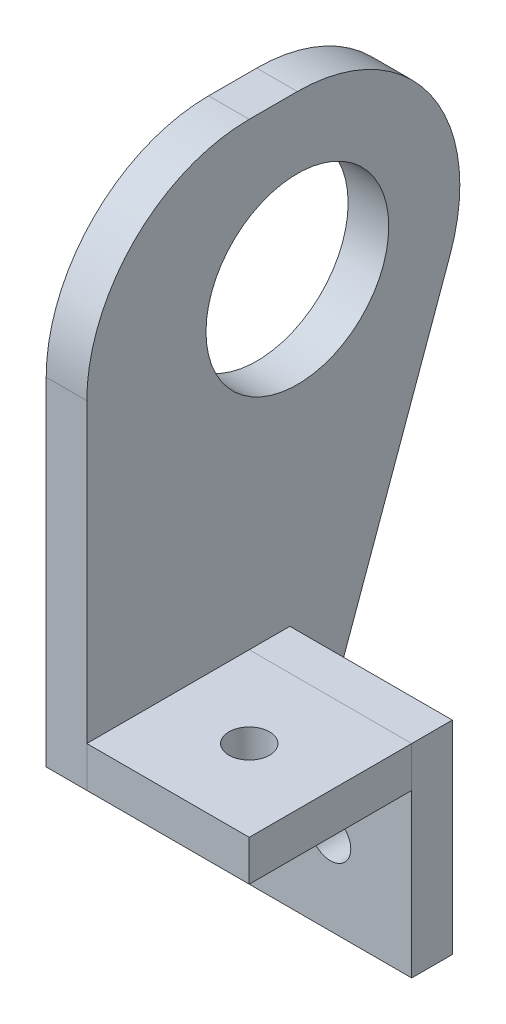
SolidWorks part; units mm, degrees
material "6061-T6 (SS)"
ref_plane "Front Plane" through (0, 0, 0) normal (0, 0, 1) x (1, 0, 0)
ref_plane "Top Plane" through (0, 0, 0) normal (0, 1, 0) x (1, 0, 0)
ref_plane "Right Plane" through (0, 0, 0) normal (1, 0, 0) x (0, 0, -1)
sketch "Sketch1" plane through (0, 0, 0) normal (1, 0, 0) x (0, 0, -1)
  line L0 (0, 25.4) -> (-32.925, 25.4)
  line L1 (-32.925, 25.4) -> (-32.925, -52.775)
  line L2 (-7.525, -78.175) -> (-1.175, -78.175)
  line L3 (-1.175, -78.175) -> (23.8955, -8.6119)
  line L4 (-32.925, -52.775) -> (-32.925, 232.975) construction
  line L5 (-7.525, -78.175) -> (-32.925, -78.175) construction
  line L6 (-7.525, -78.175) -> (-7.525, -54.3625)
  line L7 (-9.1125, -52.775) -> (-32.925, -52.775)
  circle A0 centre (0, 0) radius 14.2875
  arc A1 (23.8955, -8.6119) -> (0, 25.4) centre (0, 0) ccw
  arc A2 (-7.525, -54.3625) -> (-9.1125, -52.775) centre (-9.1125, -54.3625) ccw
  point P9 (-7.525, -52.775)
  dimension "D1" = 28.575
  dimension "D2" = 25.4
  dimension "D5" = 1.5875
  dimension "D3" = 31.75
  dimension "D4" = 25.4
extrude "Boss-Extrude1" add sketch "Sketch1" along normal blind 6.35
sketch "Sketch2" plane through (6.35, 0, 0) normal (1, 0, 0) x (0, 0, -1)
  line L0 (-7.525, -54.3625) -> (-7.525, -78.175) construction
  line L1 (-32.925, -52.775) -> (-7.525, -52.775)
  line L2 (-32.925, -52.775) -> (-32.925, -46.425)
  line L3 (-32.925, -46.425) -> (-7.525, -46.425)
  line L4 (-7.525, -52.775) -> (-7.525, -46.425)
  dimension "D1" = 6.35
extrude "Boss-Extrude2" add sketch "Sketch2" along normal blind 25.4 separate body
fillet "Fillet1" radius 25.4 1 edges at (3.175, 25.4, 32.925)
sketch "Sketch3" plane through (6.35, 0, 0) normal (1, 0, 0) x (0, 0, -1)
  line L1 (-1.175, -78.175) -> (-7.525, -78.175)
  line L2 (-1.175, -78.175) -> (-1.175, -46.425)
  line L3 (-1.175, -46.425) -> (-7.525, -46.425)
  line L4 (-7.525, -78.175) -> (-7.525, -46.425)
extrude "Boss-Extrude3" add sketch "Sketch3" along normal blind 25.4 separate body
sketch "Sketch4" plane through (0, -52.775, 0) normal (0, -1, 0) x (1, 0, 0)
  line L0 (19.05, 32.925) -> (19.05, 7.525) construction
  line L1 (31.75, 32.925) -> (6.35, 32.925) construction
  line L2 (31.75, 7.525) -> (6.35, 7.525) construction
  circle A0 centre (19.05, 20.225) radius 3.175
  dimension "D1" = 6.35
extrude "Cut-Extrude1" cut sketch "Sketch4" against normal through all
sketch "Sketch5" plane through (0, 0, 7.525) normal (0, 0, 1) x (1, 0, 0)
  line L0 (6.35, -52.775) -> (31.75, -78.175) construction
  circle A0 centre (19.05, -65.475) radius 3.175
  dimension "D1" = 6.35
extrude "Cut-Extrude2" cut sketch "Sketch5" against normal through all
sketch "Sketch6" [suppressed] plane through (0, 0, 0) normal (1, 0, 0) x (0, 0, -1)
  line L0 (-32.925, -52.775) -> (-7.525, -52.775)
  line L1 (-32.925, -52.775) -> (-7.525, -52.775) construction
  line L2 (0, 25.4) -> (-32.925, 25.4)
  line L3 (-32.925, 25.4) -> (-32.925, -52.775)
  line L4 (-7.525, -52.775) -> (-7.525, -48.0125)
  line L5 (-7.525, -48.0125) -> (19.338, -16.4682)
  line L6 (-32.925, -109.925) -> (-32.925, -78.175) construction
  circle A0 centre (0, 0) radius 25.4 construction
  circle A1 centre (0, 0) radius 14.2875
  arc A2 (0, 25.4) -> (19.338, -16.4682) centre (0, 0) cw
  dimension "D1" = 28.575
  dimension "D2" = 50.8
  dimension "D3" = 25.4
  dimension "D4" = 4.7625
base flange "Base-Flange2" [suppressed] sketch "Sketch6" thickness 3.175 reverse thickness direction no parameters "D1"=0.7366
edge flange "Edge-Flange1" sketch "Sketch18" flange angle 90 flange position material inside bend radius 0.7366 thickness 3.175
sketch "Sketch18" [suppressed] plane through (0, -33.725, 0) normal (0, -1, 0) x (0, 0, -1)
  line L2 (-32.925, 0) -> (-32.925, 25.4)
  line L3 (-32.925, 25.4) -> (-7.525, 25.4)
  line L4 (-7.525, 25.4) -> (-7.525, 0)
  line L5 (-32.925, 0) -> (-7.525, 0) construction
  line L6 (-32.925, 0) -> (-7.525, 0)
bend "EdgeBend1" [suppressed] bend radius 0.7366 bend angle 90 parameters "D5"=1, "D6"=10, "D7"=25.4
sketch "Sketch22" [suppressed] plane through (0, -30.55, 0) normal (0, 1, 0) x (1, 0, 0)
  line L0 (0, -32.925) -> (25.4, -7.525) construction
  circle A0 centre (12.7, -20.225) radius 3.175
  dimension "D1" = 6.35
extrude "Cut-Extrude3" [suppressed] cut sketch "Sketch22" against normal through all
edge flange "Edge-Flange2" sketch "Sketch21" flange angle 90 flange position material inside bend radius 0.7366 thickness 3.175
sketch "Sketch21" [suppressed] plane through (-3.175, -52.775, 0) normal (0, -1, 0) x (0, 0, 1)
  line L0 (32.925, 0) -> (7.525, 0) construction
  line L1 (32.925, 0) -> (7.525, 0)
  line L2 (7.525, 0) -> (7.525, 25.4)
  line L3 (7.525, 25.4) -> (32.925, 25.4)
  line L4 (32.925, 25.4) -> (32.925, 0)
bend "EdgeBend2" [suppressed] bend radius 0.7366 bend angle 90 parameters "D5"=1, "D6"=10, "D7"=25.4
sketch "Sketch23" [suppressed] plane through (0, -49.6, 0) normal (0, 1, 0) x (1, 0, 0)
  line L0 (-28.575, -7.525) -> (-3.175, -32.925) construction
  circle A0 centre (-15.875, -20.225) radius 3.175
  dimension "D1" = 6.35
extrude "Cut-Extrude4" [suppressed] cut sketch "Sketch23" against normal through all
fillet "Fillet2" [suppressed] radius 25.4
sketch "Sketch24" [suppressed] plane through (0, 0, 0) normal (1, 0, 0) x (0, 0, -1)
  line L1 (-7.525, -28.2259) -> (-2.7934, -28.2259)
  line L2 (-7.525, -28.2259) -> (-7.525, -29.262)
  line L3 (-7.525, -29.262) -> (-2.7934, -29.262)
  line L4 (-2.7934, -28.2259) -> (-2.7934, -29.262)
extrude "Cut-Extrude5" [suppressed] cut sketch "Sketch24" against normal through all
fillet "Fillet3" [suppressed] radius 25.4
fillet "Fillet4" [suppressed] radius 1.5875
sketch "Bend-Lines3" [suppressed] plane through (0, 0, 0) normal (0, 1, 0) x (1, 0, 0)
sketch "Bounding-Box3" [suppressed] plane through (0, 0, 0) normal (0, 1, 0) x (1, 0, 0)
sheet metal parameters "Sheet-Metal7" [suppressed] thickness 3.175 parameters "D1"=0.7366
flat pattern "Flat-Pattern14"
sketch "Bend-Lines4" [suppressed] plane through (0, 0, 0) normal (0, 1, 0) x (1, 0, 0)
sketch3d "Bounding-Box4" [suppressed]
  line L0 (-29.3589, -46.2064, 0) -> (-29.3589, 25.4, 0) construction
  line L1 (25.4, -46.2064, 0) -> (25.4, 25.4, 0) construction
  line L2 (-29.3589, -46.2064, 0) -> (25.4, -46.2064, 0) construction
  line L3 (-29.3589, 25.4, 0) -> (25.4, 25.4, 0) construction
sheet metal parameters "Sheet-Metal8" [suppressed] thickness 3.175 parameters "D1"=0.7366
flat pattern "Flat-Pattern14"
sketch "Bend-Lines4" [suppressed] plane through (0, 0, 0) normal (1, 0, 0) x (0, 0, -1)
  line L0 (-29.3589, -44.1201) -> (-3.9589, -44.1201) construction
  line L1 (-29.3589, -44.1201) -> (-3.9589, -44.1201) construction
sketch3d "Bounding-Box4" [suppressed]
  line L0 (-29.3589, -70.6089, 0) -> (-29.3589, 25.4, 0) construction
  line L1 (25.4, -70.6089, 0) -> (25.4, 25.4, 0) construction
  line L2 (-29.3589, -70.6089, 0) -> (25.4, -70.6089, 0) construction
  line L3 (-29.3589, 25.4, 0) -> (25.4, 25.4, 0) construction
bend of the flat pattern "Flatten-<EdgeBend1>1" [suppressed]
sheet metal parameters "Sheet-Metal9" [suppressed] thickness 3.175 parameters "D1"=0.7366
flat pattern "Flat-Pattern14"
sketch "Bend-Lines4" [suppressed] plane through (0, 0, 0) normal (1, 0, 0) x (0, 0, -1)
  line L0 (-29.3589, -44.1201) -> (-3.9589, -44.1201) construction
  line L1 (-29.3589, -44.1201) -> (-3.9589, -44.1201) construction
sketch3d "Bounding-Box4" [suppressed]
  line L0 (-29.3589, -70.6089, 0) -> (-29.3589, 25.4, 0) construction
  line L1 (25.4, -70.6089, 0) -> (25.4, 25.4, 0) construction
  line L2 (-29.3589, -70.6089, 0) -> (25.4, -70.6089, 0) construction
  line L3 (-29.3589, 25.4, 0) -> (25.4, 25.4, 0) construction
bend of the flat pattern "Flatten-<EdgeBend2>1" [suppressed]
sheet metal parameters "Sheet-Metal10" [suppressed] thickness 3.175 parameters "D1"=0.7366
flat pattern "Flat-Pattern14"
sketch "Bend-Lines4" [suppressed] plane through (0, 0, 0) normal (1, 0, 0) x (0, 0, -1)
  line L0 (-32.925, -31.6387) -> (-7.525, -31.6387) construction
  line L1 (-32.925, -31.6387) -> (-7.525, -31.6387) construction
sketch3d "Bounding-Box4" [suppressed]
  line L0 (-32.925, -58.1275, 0) -> (-32.925, 25.4, 0) construction
  line L1 (25.4, -58.1275, 0) -> (25.4, 25.4, 0) construction
  line L2 (-32.925, -58.1275, 0) -> (25.4, -58.1275, 0) construction
  line L3 (-32.925, 25.4, 0) -> (25.4, 25.4, 0) construction
bend of the flat pattern "Flatten-<EdgeBend1>1" [suppressed]
sheet metal parameters "Sheet-Metal11" [suppressed] thickness 3.175 parameters "D1"=0.7366
flat pattern "Flat-Pattern14"
sketch "Bend-Lines4" [suppressed] plane through (0, 0, 0) normal (1, 0, 0) x (0, 0, -1)
  line L0 (-32.925, -50.6887) -> (-7.525, -50.6887) construction
  line L1 (-32.925, -50.6887) -> (-7.525, -50.6887) construction
sketch3d "Bounding-Box4" [suppressed]
  line L0 (-32.925, -77.1775, 0) -> (-32.925, 25.4, 0) construction
  line L1 (25.4, -77.1775, 0) -> (25.4, 25.4, 0) construction
  line L2 (-32.925, -77.1775, 0) -> (25.4, -77.1775, 0) construction
  line L3 (-32.925, 25.4, 0) -> (25.4, 25.4, 0) construction
bend of the flat pattern "Flatten-<EdgeBend2>1" [suppressed]
sheet metal parameters "Sheet-Metal14" [suppressed] thickness 3.175 parameters "D1"=0.7366
flat pattern "Flat-Pattern14"
sketch "Bend-Lines4" [suppressed] plane through (0, 0, 0) normal (1, 0, 0) x (0, 0, -1)
  line L2 (-32.925, -31.6387) -> (-7.525, -31.6387) construction
  line L3 (-32.925, -31.6387) -> (-7.525, -31.6387) construction
sketch3d "Bounding-Box4" [suppressed]
  line L0 (-32.925, -58.1275, 0) -> (-32.925, 25.4, 0) construction
  line L1 (25.4, -58.1275, 0) -> (25.4, 25.4, 0) construction
  line L2 (-32.925, -58.1275, 0) -> (25.4, -58.1275, 0) construction
  line L3 (-32.925, 25.4, 0) -> (25.4, 25.4, 0) construction
bend of the flat pattern "Flatten-<EdgeBend2>2" [suppressed]
